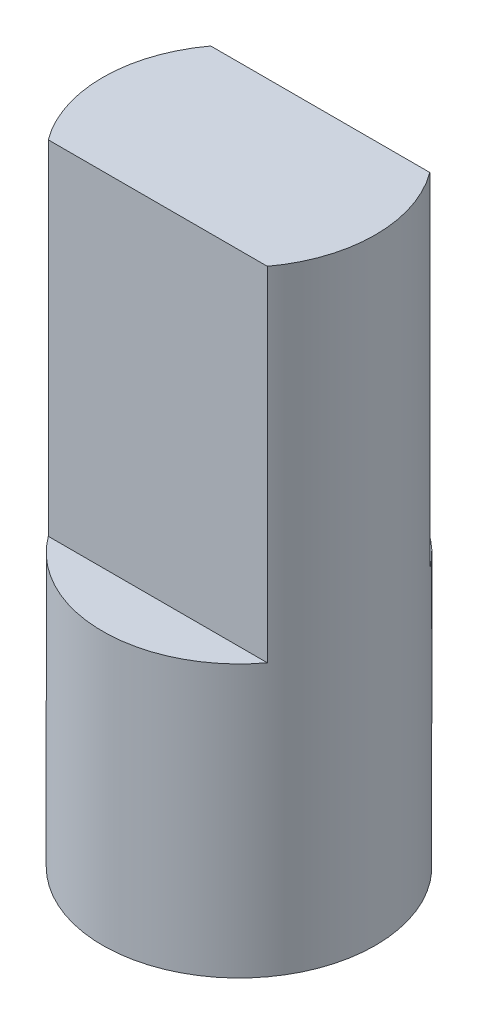
SolidWorks part; units mm, degrees
ref_plane "Front Plane" through (0, 0, 0) normal (0, 0, 1) x (1, 0, 0)
ref_plane "Top Plane" through (0, 0, 0) normal (0, 1, 0) x (1, 0, 0)
ref_plane "Right Plane" through (0, 0, 0) normal (1, 0, 0) x (0, 0, -1)
sketch "Sketch2" plane through (0, 0, 0) normal (0, 1, 0) x (1, 0, 0)
  line L0 (-1.9685, 1.4605) -> (1.9685, 1.4605)
  line L2 (1.9685, -1.4605) -> (-1.9685, -1.4605)
  arc A0 (-1.9685, 1.4605) -> (-1.9685, -1.4605) centre (0, 0) ccw
  arc A1 (1.9685, -1.4605) -> (1.9685, 1.4605) centre (0, 0) ccw
  dimension "D1" = 4.9022
  dimension "D2" = 2.921
extrude "Boss-Extrude1" add sketch "Sketch2" against normal blind 6.1722
sketch "Sketch3" plane through (0, -6.1722, 0) normal (0, -1, 0) x (1, 0, 0)
  circle A0 centre (0, 0) radius 2.4511
  dimension "D1" = 4.9022
extrude "Boss-Extrude2" add sketch "Sketch3" along normal blind 4.8895
